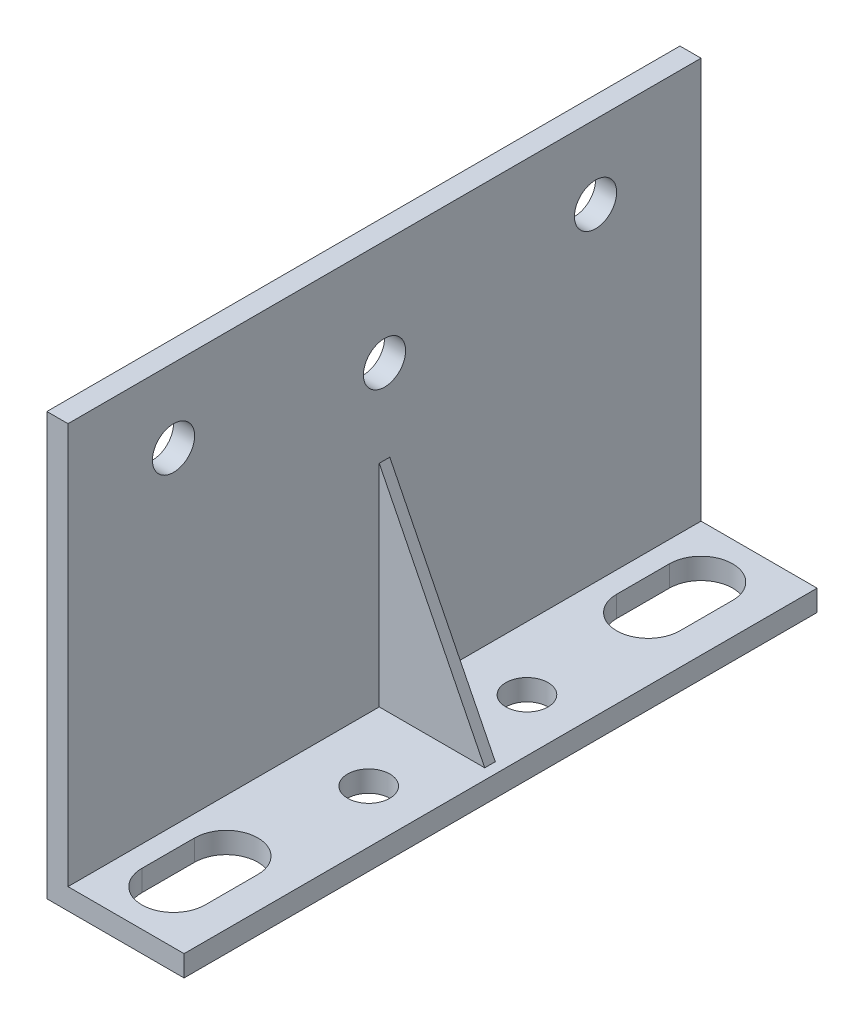
SolidWorks part; units mm, degrees
material "Alloy Steel (SS)"
ref_plane "Front Plane" through (0, 0, 0) normal (0, 0, 1) x (1, 0, 0)
ref_plane "Top Plane" through (0, 0, 0) normal (0, 1, 0) x (1, 0, 0)
ref_plane "Right Plane" through (0, 0, 0) normal (1, 0, 0) x (0, 0, -1)
sketch "Sketch1" plane through (0, 0, 0) normal (0, 0, 1) x (1, 0, 0)
  line L0 (0, 0) -> (-11, 0)
  line L1 (-11, 0) -> (-11, 38)
  line L2 (-11, 38) -> (-13, 38)
  line L3 (-13, 38) -> (-13, -2)
  line L4 (-13, -2) -> (0, -2)
  line L5 (0, -2) -> (0, 0)
  dimension "D1" = 40
  dimension "13" = 13
  dimension "D2" = 2
  dimension "D3" = 2
extrude "Boss-Extrude1" add sketch "Sketch1" along normal blind 60
ref_plane "Plane1" through (0, 0, 30) normal (0, 0, 1) x (1, 0, 0)
sketch "Sketch4" plane through (0, 0, 30) normal (0, 0, 1) x (1, 0, 0)
  line L0 (-11, 20) -> (-1, 0)
  line L1 (-11, 0) -> (-11, 38) construction
  line L2 (0, 0) -> (-11, 0) construction
  line L3 (-11, 20) -> (-11, 0)
  line L4 (-11, 0) -> (-1, 0)
  dimension "D1" = 1
  dimension "D2" = 20
extrude "Boss-Extrude2" add sketch "Sketch4" along normal mid plane 1
sketch "Sketch5" plane through (0, 0, 0) normal (0, 1, 0) x (1, 0, 0)
  line L0 (-6, -5) -> (-6, -10) construction
  line L1 (-3, -5) -> (-3, -10)
  line L2 (-9, -5) -> (-9, -10)
  line L3 (-13, -60) -> (-13, 0) construction
  arc A0 (-3, -5) -> (-9, -5) centre (-6, -5) ccw
  arc A1 (-9, -10) -> (-3, -10) centre (-6, -10) ccw
  point P2 (-6, -7.5)
  dimension "D3" = 3
  dimension "D1" = 7
  dimension "D2" = 5
  dimension "D4" = 5
extrude "Cut-Extrude1" cut sketch "Sketch5" against normal up to next (2 mm away)
mirror "Mirror1" about plane through (0, 0, 30) normal (0, 0, 1) of "Cut-Extrude1"
sketch "Sketch6" plane through (-13, 0, 0) normal (1, 0, 0) x (0, 0, -1)
  line L1 (-60, 0) -> (-60, 38) construction
  line L2 (0, 0) -> (0, 38) construction
  line L3 (-60, 38) -> (0, 38) construction
  circle A0 centre (-50, 31) radius 2
  circle A1 centre (-10, 31) radius 2
  dimension "D4" = 4
  dimension "D1" = 10
  dimension "D2" = 10
  dimension "D3" = 7
extrude "Cut-Extrude2" cut sketch "Sketch6" along normal up to next
sketch "Sketch7" plane through (-11, 0, 0) normal (1, 0, 0) x (0, 0, -1)
  line L0 (0, 0) -> (0, 38) construction
  line L2 (-60, -2) -> (0, -2) construction
  circle A0 centre (-30, 28) radius 2
  dimension "D1" = 4
  dimension "D2" = 30
  dimension "D3" = 30
  dimension "D4" = 30
extrude "Cut-Extrude3" cut sketch "Sketch7" against normal up to next
sketch "Sketch8" plane through (0, 0, 0) normal (0, 1, 0) x (1, 0, 0)
  line L0 (0, -60) -> (0, 0) construction
  line L1 (-1, -30.5) -> (-11, -30.5) construction
  circle A0 centre (-5, -37.5) radius 2
  dimension "D1" = 5
  dimension "D3" = 4
  dimension "D2" = 7
extrude "Cut-Extrude4" cut sketch "Sketch8" against normal up to next (2 mm away)
mirror "Mirror2" about plane through (0, 0, 30) normal (0, 0, 1) of "Cut-Extrude4"
